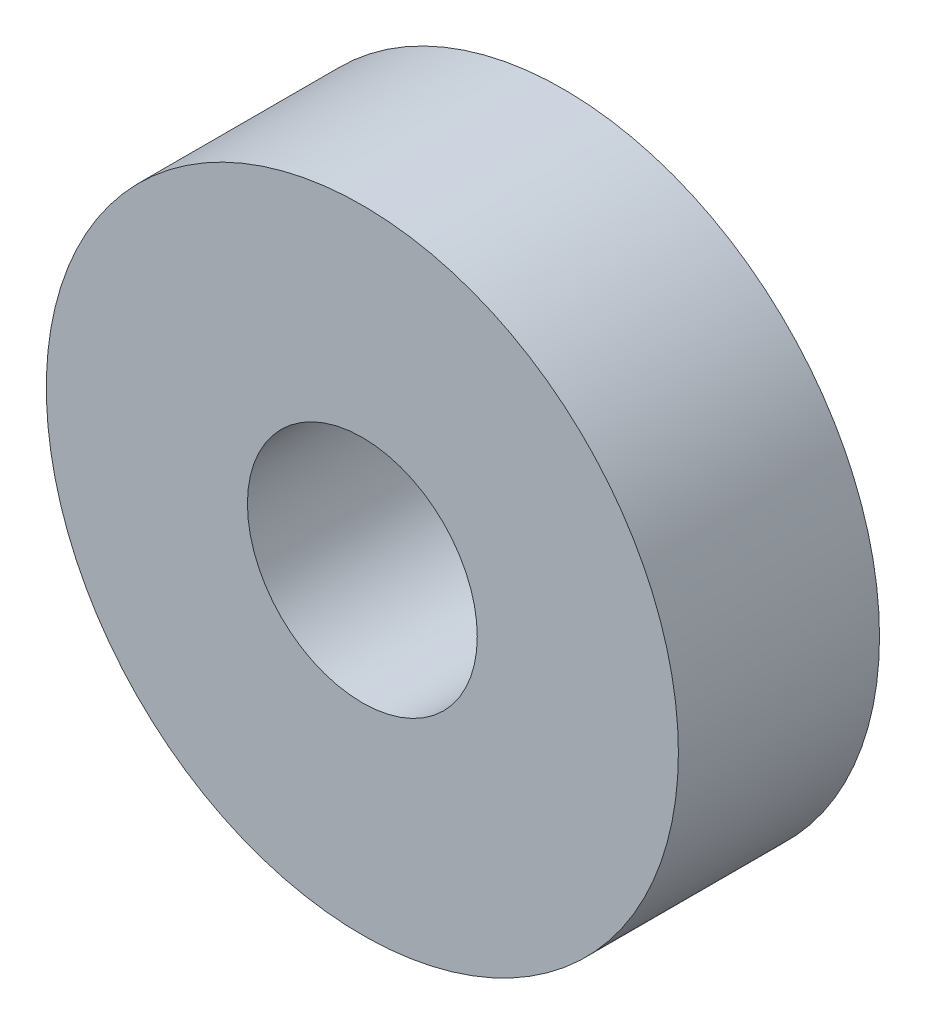
SolidWorks part; units mm, degrees
ref_plane "Alzado" through (0, 0, 0) normal (0, 0, 1) x (1, 0, 0)
ref_plane "Planta" through (0, 0, 0) normal (0, 1, 0) x (1, 0, 0)
ref_plane "Vista lateral" through (0, 0, 0) normal (1, 0, 0) x (0, 0, -1)
sketch "Croquis1" plane through (0, 0, 0) normal (0, 0, 1) x (1, 0, 0)
  circle A0 centre (0, 0) radius 4
  circle A1 centre (0, 0) radius 11
  dimension "D1" = 8
  dimension "D2" = 22
extrude "Saliente-Extruir1" add sketch "Croquis1" along normal blind 7
